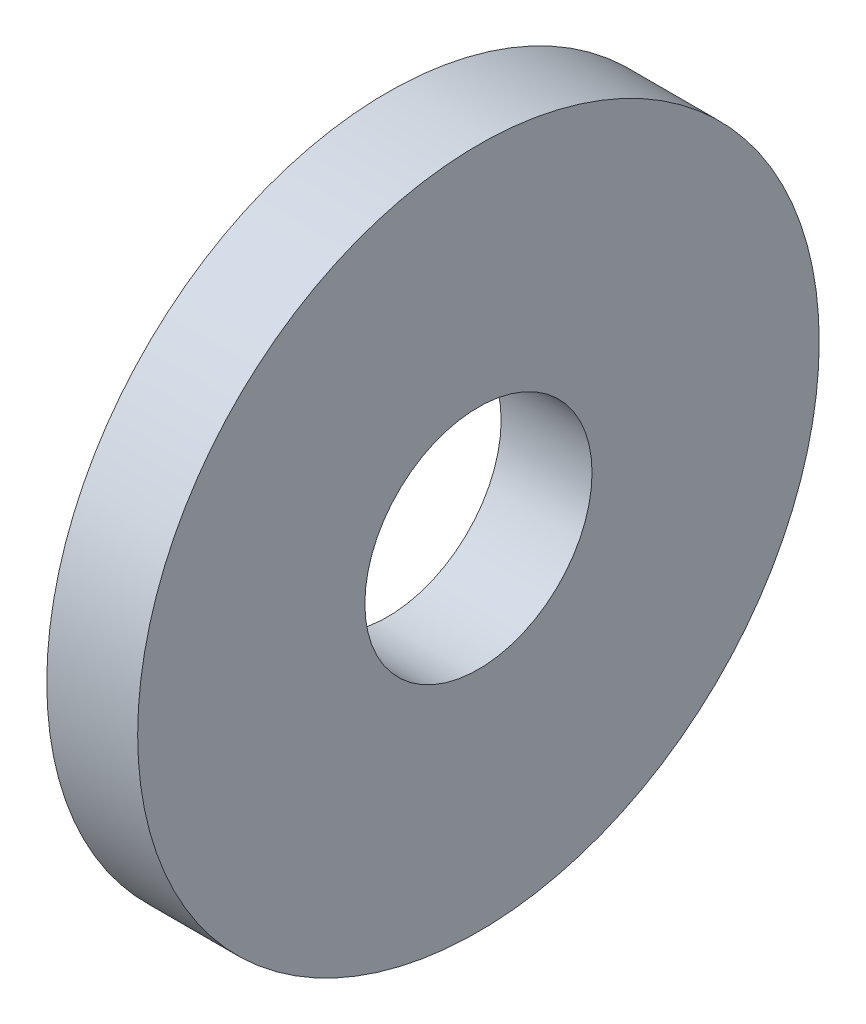
SolidWorks part; units mm, degrees
ref_plane "前视基准面" through (0, 0, 0) normal (0, 0, 1) x (1, 0, 0)
ref_plane "上视基准面" through (0, 0, 0) normal (0, 1, 0) x (1, 0, 0)
ref_plane "右视基准面" through (0, 0, 0) normal (1, 0, 0) x (0, 0, -1)
sketch "草图1" plane through (0, 0, 0) normal (1, 0, 0) x (0, 0, -1)
  circle A0 centre (0, 0) radius 15
  circle A1 centre (0, 0) radius 5
extrude "凸台-拉伸1" add sketch "草图1" along normal blind 4
